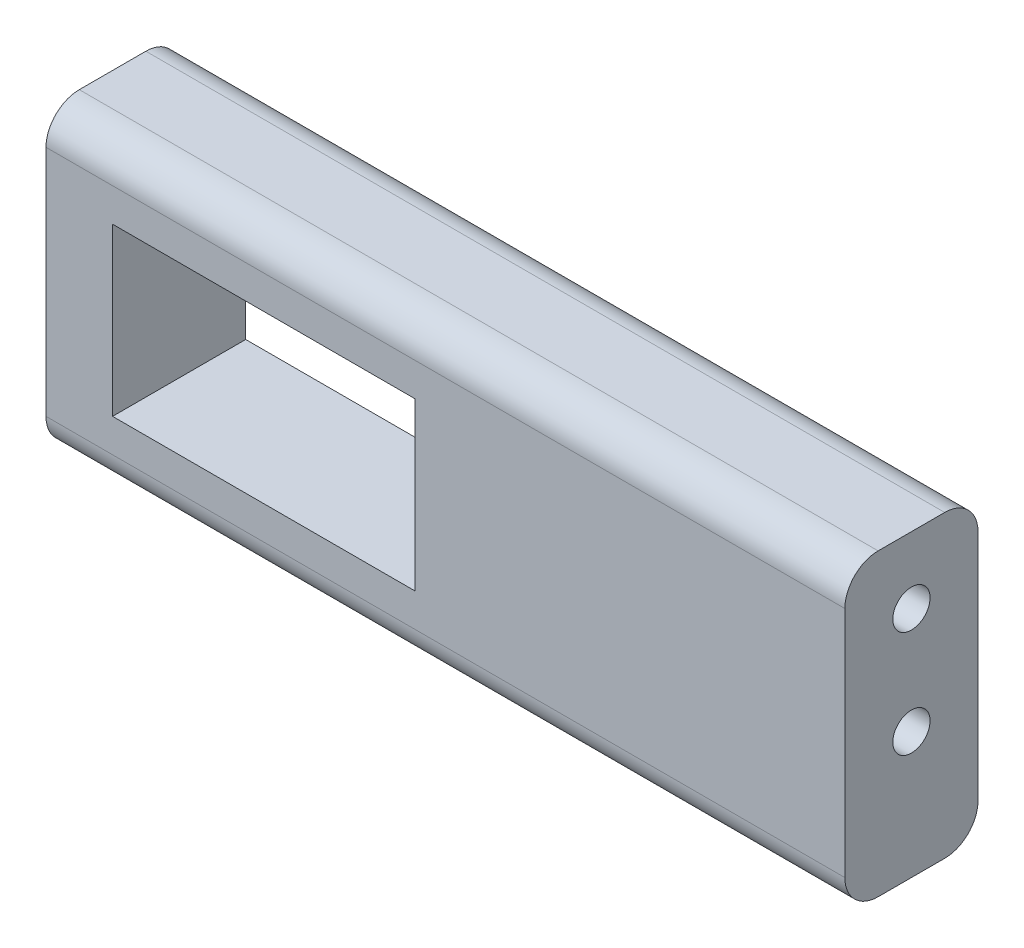
SolidWorks part; units mm, degrees
ref_plane "Plano frontal" through (0, 0, 0) normal (0, 0, 1) x (1, 0, 0)
ref_plane "Plano superior" through (0, 0, 0) normal (0, 1, 0) x (1, 0, 0)
ref_plane "Plano direito" through (0, 0, 0) normal (1, 0, 0) x (0, 0, -1)
sketch "Esboço1" plane through (0, 0, 0) normal (0, 0, 1) x (1, 0, 0)
  line L1 (-10.2055, 7.7579) -> (12.4945, 7.7579)
  line L2 (-10.2055, 7.7579) -> (-10.2055, -4.7421)
  line L3 (-10.2055, -4.7421) -> (12.4945, -4.7421)
  line L4 (12.4945, 7.7579) -> (12.4945, -4.7421)
  line L5 (-15.2055, 12.7579) -> (44.7945, 12.7579)
  line L6 (-15.2055, 12.7579) -> (-15.2055, -9.7421)
  line L7 (-15.2055, -9.7421) -> (44.7945, -9.7421)
  line L8 (44.7945, 12.7579) -> (44.7945, -9.7421)
  dimension "D1" = 22.7
  dimension "D2" = 12.5
  dimension "D3" = 60
  dimension "D4" = 5
  dimension "D5" = 5
  dimension "D6" = 5
extrude "Ressalto-extrusão1" add sketch "Esboço1" along normal blind 10
sketch "Esboço3" plane through (44.7945, 0, 0) normal (1, 0, 0) x (0, 0, -1)
  line L0 (-10, 12.7579) -> (0, 12.7579) construction
  line L1 (0, -9.7421) -> (0, 12.7579) construction
  circle A0 centre (-5, 7.7579) radius 1.4
  circle A1 centre (-5, -0.2421) radius 1.4
  dimension "D1" = 2.8
  dimension "D2" = 5
  dimension "D3" = 5
  dimension "D4" = 5
  dimension "D5" = 2.8
  dimension "D6" = 8
extrude "Corte-extrusão2" cut sketch "Esboço3" against normal blind 20
sketch "Esboço4" plane through (-15.2055, 0, 0) normal (-1, 0, 0) x (0, 0, 1)
  line L0 (10, 12.7579) -> (0, 12.7579) construction
  line L1 (0, 12.7579) -> (0, -9.7421) construction
  circle A0 centre (5, 7.7579) radius 1.4
  circle A1 centre (5, -0.2421) radius 1.4
  dimension "D1" = 2.8
  dimension "D2" = 2.8
  dimension "D3" = 5
  dimension "D4" = 5
  dimension "D5" = 5
  dimension "D6" = 8
extrude "Corte-extrusão3" cut sketch "Esboço4" against normal blind 3
fillet "Filete1" radius 2.5 4 edges at (14.7945, -9.7421, 10) (14.7945, 12.7579, 10) (14.7945, -9.7421, 0) (14.7945, 12.7579, 0)
